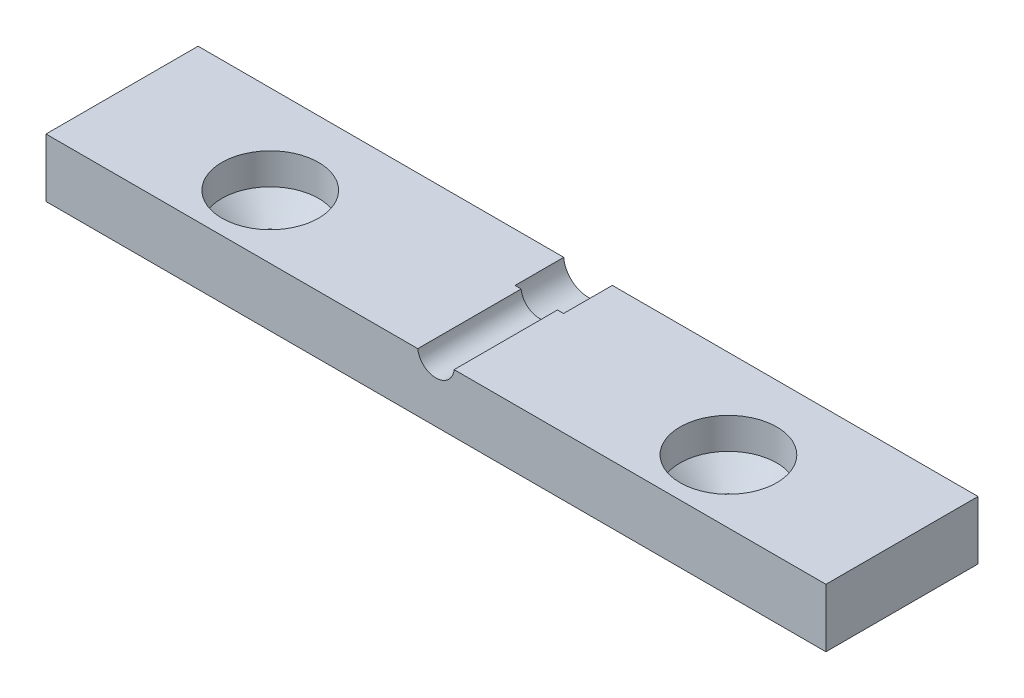
SolidWorks part; units mm, degrees
ref_plane "Front Plane" through (0, 0, 0) normal (0, 0, 1) x (1, 0, 0)
ref_plane "Top Plane" through (0, 0, 0) normal (0, 1, 0) x (1, 0, 0)
ref_plane "Right Plane" through (0, 0, 0) normal (1, 0, 0) x (0, 0, -1)
sketch "Sketch1" plane through (0, 0, 0) normal (0, 1, 0) x (1, 0, 0)
  line L1 (50.8, -9.906) -> (-50.8, -9.906)
  line L2 (50.8, -9.906) -> (50.8, 9.906)
  line L3 (50.8, 9.906) -> (-50.8, 9.906)
  line L4 (-50.8, -9.906) -> (-50.8, 9.906)
  line L5 (50.8, -9.906) -> (-50.8, 9.906) construction
  line L6 (50.8, 9.906) -> (-50.8, -9.906) construction
  point P0 (0, 0)
  dimension "D1" = 101.6
  dimension "D2" = 19.812
extrude "Boss-Extrude1" add sketch "Sketch1" along normal blind 3.81
hole_wizard "CSK for M6 Countersunk Flat Head Screw1" positions "Sketch2" profile "Sketch4" countersink size "M6" standard "HASCO Metric" end condition through all
sketch "Sketch2" plane through (0, 3.81, 0) normal (0, 1, 0) x (1, 0, 0)
  line L0 (-29.845, -1.651) -> (29.845, -1.651)
  line L1 (0, 0) -> (0, -1.651) construction
  line L3 (-50.8, -9.906) -> (50.8, -9.906) construction
  point P0 (-29.845, -1.651)
  point P2 (29.845, -1.651)
  point P20 (0, 0)
  dimension "D1" = 59.69
  dimension "D2" = 8.255
sketch "Sketch4" plane through (-29.845, 3.81, 1.651) normal (1, 0, 0) x (0, 0, 1)
  line L0 (0, 0) -> (0, 3.81)
  line L1 (0, 3.81) -> (3.5, 3.81)
  line L2 (3.5, 3.81) -> (3.5, 3.054)
  line L3 (3.5, 3.054) -> (6.3, 0.254)
  line L4 (6.3, 0.254) -> (6.3, 0)
  line L6 (6.3, 0) -> (0, 0)
  line L7 (-3.5, 3.054) -> (-6.3, 0.254) construction
  line L11 (0, -6.35) -> (0, 107.95) construction
  dimension "Thru Hole Dia." = 7
  dimension "Thru Hole Depth" = 3.81
  dimension "C'Sink Dia." = 12.6
  dimension "C'Sink Angle" = 90
  dimension "Head Clearance" = 0.254
sketch "Sketch5" plane through (0, 3.81, 0) normal (0, 1, 0) x (1, 0, 0)
  line L4 (-50.8, 9.906) -> (-50.8, -9.906)
  line L5 (-50.8, -9.906) -> (50.8, -9.906)
  line L6 (50.8, -9.906) -> (50.8, 9.906)
  line L7 (50.8, 9.906) -> (-50.8, 9.906)
  line L8 (-50.8, 9.906) -> (-50.8, -9.906)
  line L9 (-50.8, -9.906) -> (50.8, -9.906)
  line L10 (50.8, -9.906) -> (50.8, 9.906)
  line L11 (50.8, 9.906) -> (-50.8, 9.906)
  circle A0 centre (-29.845, -1.651) radius 6.3 construction
  circle A1 centre (-29.845, -1.651) radius 6.3
  circle A2 centre (29.845, -1.651) radius 6.3 construction
  circle A3 centre (29.845, -1.651) radius 6.3
  dimension "D1" = 0
extrude "Boss-Extrude2" add sketch "Sketch5" along normal offset from surface (3.81 mm away) 7.62 up to face at (-29.845, 0, 5.151)
sketch "Sketch6" plane through (0, 0, -9.906) normal (0, 0, -1) x (-1, 0, 0)
  line L0 (0, 0) -> (0, 7.874) construction
  line L1 (-50.8, 0) -> (50.8, 0) construction
  line L2 (-50.8, 7.62) -> (50.8, 7.62) construction
  circle A0 centre (0, 7.874) radius 3.175
  dimension "D1" = 6.35
  dimension "D2" = 0.254
extrude "Cut-Extrude1" cut sketch "Sketch6" against normal blind 6.35
sketch "Sketch7" plane through (0, 0, -3.556) normal (0, 0, -1) x (-1, 0, 0)
  line L1 (3.1648, 7.62) -> (-3.1648, 7.62)
  line L2 (3.1648, 7.62) -> (-3.1648, 7.62)
  circle A0 centre (0, 7.874) radius 2.3813
  arc A1 (-3.1648, 7.62) -> (3.1648, 7.62) centre (0, 7.874) ccw
  arc A2 (-3.1648, 7.62) -> (3.1648, 7.62) centre (0, 7.874) ccw
  dimension "D2" = 4.7625
  dimension "D1" = 0
extrude "Cut-Extrude2" cut sketch "Sketch7" against normal through all both and the other way through all contours L2 A0 | L2 A0
